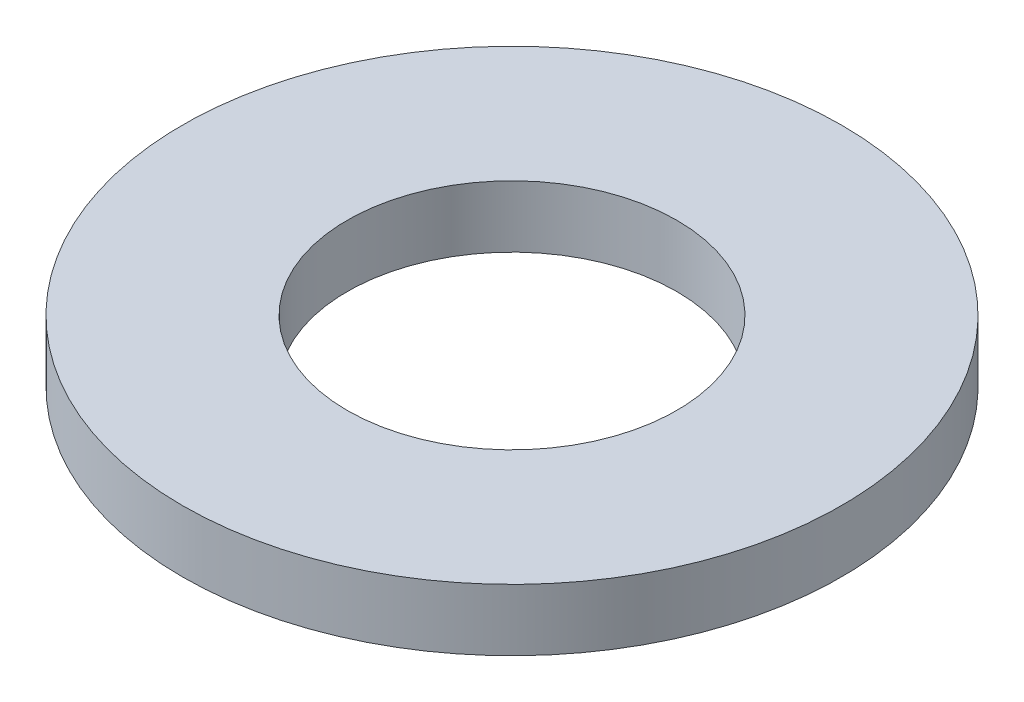
SolidWorks part; units mm, degrees
ref_plane "前视基准面" through (0, 0, 0) normal (0, 0, 1) x (1, 0, 0)
ref_plane "上视基准面" through (0, 0, 0) normal (0, 1, 0) x (1, 0, 0)
ref_plane "右视基准面" through (0, 0, 0) normal (1, 0, 0) x (0, 0, -1)
sketch "草图1" plane through (0, 0, 0) normal (0, 1, 0) x (1, 0, 0)
  circle A0 centre (-2.446, 0.7262) radius 8
  circle A1 centre (-2.446, 0.7262) radius 4
  dimension "D1" = 16
  dimension "D2" = 8
extrude "凸台-拉伸1" add sketch "草图1" along normal blind 1.5
